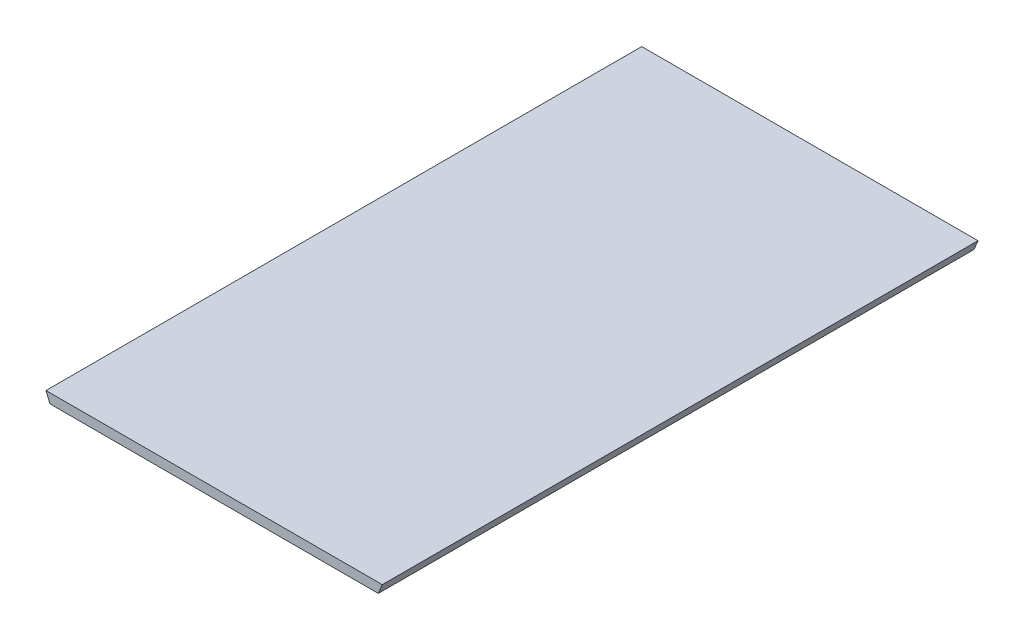
SolidWorks part; units mm, degrees
ref_plane "Plan de face" through (0, 0, 0) normal (0, 0, 1) x (1, 0, 0)
ref_plane "Plan de dessus" through (0, 0, 0) normal (0, 1, 0) x (1, 0, 0)
ref_plane "Plan de droite" through (0, 0, 0) normal (1, 0, 0) x (0, 0, -1)
sketch "Esquisse1" plane through (0, 0, 0) normal (0, 1, 0) x (1, 0, 0)
  line L1 (0, 0) -> (170.86, 0)
  line L2 (0, 0) -> (0, 310)
  line L3 (0, 310) -> (170.86, 310)
  line L4 (170.86, 0) -> (170.86, 310)
  dimension "D1" = 310
  dimension "D2" = 170.86
extrude "Boss.-Extru.1" add sketch "Esquisse1" along normal blind 5
sketch "Esquisse3" plane through (0, 0, -310) normal (0, 0, -1) x (-1, 0, 0)
  line L0 (2.07, 5) -> (-172.93, 5)
  line L1 (0, 0) -> (-170.86, 0)
  line L2 (-170.86, 5) -> (0, 5) construction
  line L3 (-172.93, 5) -> (-170.86, 0)
  line L4 (0, 0) -> (2.07, 5)
  point P6 (-85.43, 5)
  point P7 (-85.43, 0)
  dimension "D1" = 175
extrude "Boss.-Extru.2" add sketch "Esquisse3" against normal blind 310
